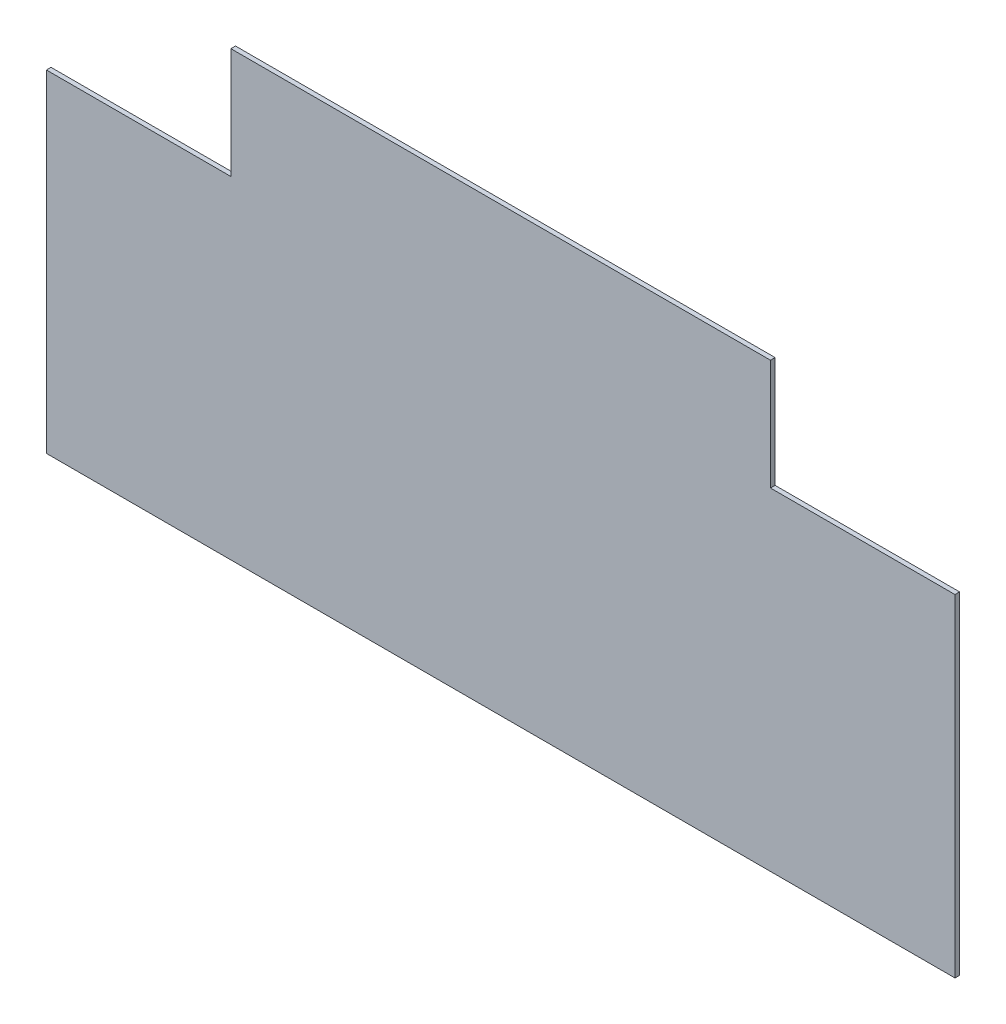
SolidWorks part; units mm, degrees
ref_plane "Front Plane" through (0, 0, 0) normal (0, 0, 1) x (1, 0, 0)
ref_plane "Top Plane" through (0, 0, 0) normal (0, 1, 0) x (1, 0, 0)
ref_plane "Right Plane" through (0, 0, 0) normal (1, 0, 0) x (0, 0, -1)
sketch "Sketch1" plane through (0, 0, 0) normal (0, 0, 1) x (1, 0, 0)
  line L0 (498.475, 228.6) -> (625.475, 228.6)
  line L1 (0, 0) -> (625.475, 0)
  line L2 (0, 0) -> (0, 228.6)
  line L3 (0, 228.6) -> (127, 228.6)
  line L4 (625.475, 0) -> (625.475, 228.6)
  line L6 (127, 228.6) -> (127, 304.8)
  line L7 (127, 304.8) -> (498.475, 304.8)
  line L8 (498.475, 228.6) -> (498.475, 304.8)
  dimension "D1" = 625.475
  dimension "D2" = 228.6
  dimension "D3" = 127
  dimension "D4" = 127
  dimension "D5" = 76.2
extrude "Boss-Extrude1" add sketch "Sketch1" along normal blind 3.175
